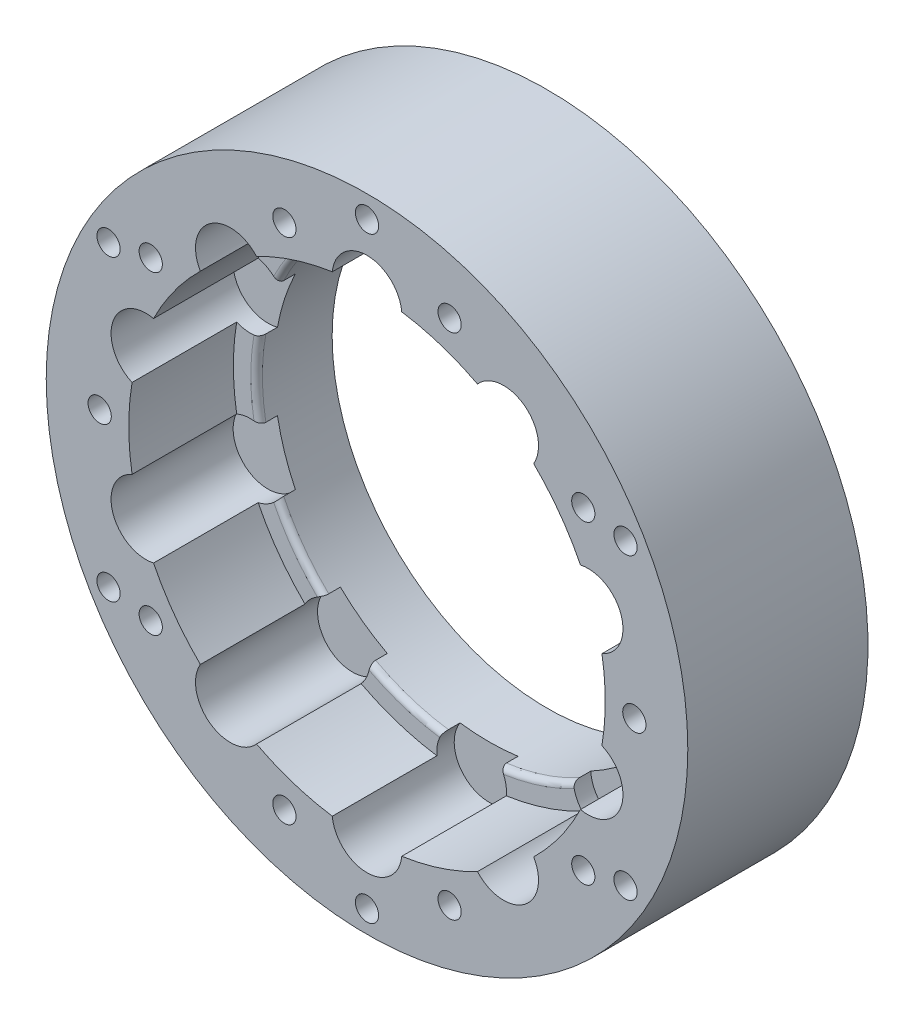
SolidWorks part; units mm, degrees
ref_plane "前视基准面" through (0, 0, 0) normal (0, 0, 1) x (1, 0, 0)
ref_plane "上视基准面" through (0, 0, 0) normal (0, 1, 0) x (1, 0, 0)
ref_plane "右视基准面" through (0, 0, 0) normal (1, 0, 0) x (0, 0, -1)
sketch "草图1" plane through (0, 0, 0) normal (0, 0, 1) x (1, 0, 0)
  circle A0 centre (0, 0) radius 27.6
  circle A1 centre (0, 0) radius 20 construction
  arc A2 (2.9916, 19.775) -> (-2.9916, 19.775) centre (0, 20) ccw
  arc A3 (-2.9916, 19.775) -> (-9.2032, 17.7567) centre (0, 0) ccw
  arc A4 (14.0437, 14.2399) -> (9.2032, 17.7567) centre (11.7557, 16.1803) ccw
  arc A5 (19.7316, 3.2657) -> (17.8827, 8.9559) centre (19.0211, 6.1803) ccw
  arc A6 (17.8827, -8.9559) -> (19.7316, -3.2657) centre (19.0211, -6.1803) ccw
  arc A7 (9.2032, -17.7567) -> (14.0437, -14.2399) centre (11.7557, -16.1803) ccw
  arc A8 (-2.9916, -19.775) -> (2.9916, -19.775) centre (0, -20) ccw
  arc A9 (-14.0437, -14.2399) -> (-9.2032, -17.7567) centre (-11.7557, -16.1803) ccw
  arc A10 (-19.7316, -3.2657) -> (-17.8827, -8.9559) centre (-19.0211, -6.1803) ccw
  arc A11 (-17.8827, 8.9559) -> (-19.7316, 3.2657) centre (-19.0211, 6.1803) ccw
  arc A12 (-9.2032, 17.7567) -> (-14.0437, 14.2399) centre (-11.7557, 16.1803) ccw
  arc A13 (-14.0437, 14.2399) -> (-17.8827, 8.9559) centre (0, 0) ccw
  arc A14 (-19.7316, 3.2657) -> (-19.7316, -3.2657) centre (0, 0) ccw
  arc A15 (-17.8827, -8.9559) -> (-14.0437, -14.2399) centre (0, 0) ccw
  arc A16 (-9.2032, -17.7567) -> (-2.9916, -19.775) centre (0, 0) ccw
  arc A17 (2.9916, -19.775) -> (9.2032, -17.7567) centre (0, 0) ccw
  arc A18 (14.0437, -14.2399) -> (17.8827, -8.9559) centre (0, 0) ccw
  arc A19 (19.7316, -3.2657) -> (19.7316, 3.2657) centre (0, 0) ccw
  arc A20 (17.8827, 8.9559) -> (14.0437, 14.2399) centre (0, 0) ccw
  arc A21 (9.2032, 17.7567) -> (2.9916, 19.775) centre (0, 0) ccw
  point P36 (0, 0)
  dimension "D1" = 55.2
  dimension "D2" = 40
  dimension "D3" = 6
  dimension "D4" = 10
extrude "凸台-拉伸1" add sketch "草图1" along normal blind 9
sketch "草图2" plane through (0, 0, 0) normal (0, 0, -1) x (-1, 0, 0)
  circle A0 centre (0, 0) radius 27.6
extrude "凸台-拉伸2" add sketch "草图2" along normal blind 3.5
sketch "草图3" plane through (0, 0, 0) normal (0, 0, 1) x (1, 0, 0)
  circle A0 centre (0, 20) radius 3
  circle A1 centre (11.7557, 16.1803) radius 3
  circle A2 centre (19.0211, 6.1803) radius 3
  circle A3 centre (19.0211, -6.1803) radius 3
  circle A4 centre (11.7557, -16.1803) radius 3
  circle A5 centre (0, -20) radius 3
  circle A6 centre (-11.7557, -16.1803) radius 3
  circle A7 centre (-19.0211, -6.1803) radius 3
  circle A8 centre (-19.0211, 6.1803) radius 3
  circle A9 centre (-11.7557, 16.1803) radius 3
  point P23 (0, 0)
  dimension "D1" = 10
extrude "切除-拉伸1" cut sketch "草图3" against normal blind 1.5
sketch "草图4" plane through (0, 0, 9) normal (0, 0, 1) x (1, 0, 0)
  line L0 (0, 0) -> (6.1803, 19.0211) construction
  line L1 (6.1803, 19.0211) -> (7.9356, 24.4231) construction
  arc A0 (9.2032, 17.7567) -> (2.9916, 19.775) centre (0, 0) ccw construction
  circle A1 centre (7.9356, 24.4231) radius 1
  circle A2 centre (20.7756, 15.0943) radius 1
  circle A3 centre (25.68, 0) radius 1
  circle A4 centre (20.7756, -15.0943) radius 1
  circle A5 centre (7.9356, -24.4231) radius 1
  circle A6 centre (-7.9356, -24.4231) radius 1
  circle A7 centre (-20.7756, -15.0943) radius 1
  circle A8 centre (-25.68, 0) radius 1
  circle A9 centre (-20.7756, 15.0943) radius 1
  circle A10 centre (-7.9356, 24.4231) radius 1
  point P28 (0, 0)
  dimension "D2" = 2
  dimension "D1" = 5.68
  dimension "D3" = 10
extrude "切除-拉伸2" cut sketch "草图4" against normal through all both and the other way through all
sketch "草图7" plane through (0, 0, -1.5) normal (0, 0, 1) x (1, 0, 0)
  circle A0 centre (0, 0) radius 18.5
  dimension "D1" = 37
extrude "切除-拉伸4" cut sketch "草图7" against normal blind 12.5
sketch "草图9" plane through (0, 0, -1.5) normal (0, 0, -1) x (-1, 0, 0)
  circle A0 centre (0, 0) radius 18.5
extrude "切除-拉伸6" cut sketch "草图9" against normal through all
sketch "草图10" plane through (0, 0, -3.5) normal (0, 0, -1) x (-1, 0, 0)
  circle A0 centre (-7.9356, 24.4231) radius 1
  circle A1 centre (7.9356, 24.4231) radius 1
  circle A2 centre (20.7756, 15.0943) radius 1
  circle A3 centre (25.68, 0) radius 1
  circle A4 centre (20.7756, -15.0943) radius 1
  circle A5 centre (7.9356, -24.4231) radius 1
  circle A6 centre (-7.9356, -24.4231) radius 1
  circle A7 centre (-20.7756, -15.0943) radius 1
  circle A8 centre (-25.68, 0) radius 1
  circle A9 centre (-20.7756, 15.0943) radius 1
  circle A10 centre (0, 0) radius 18.5
  circle A11 centre (0, 0) radius 27.6
  point P23 (0, 0)
  dimension "D1" = 10
extrude "凸台-拉伸4" add sketch "草图10" along normal blind 2
sketch "草图11" plane through (0, 0, -5.5) normal (0, 0, -1) x (-1, 0, 0)
  circle A1 centre (-7.9356, 24.4231) radius 1
  circle A2 centre (7.9356, 24.4231) radius 1
  circle A3 centre (20.7756, 15.0943) radius 1
  circle A4 centre (25.68, 0) radius 1
  circle A5 centre (20.7756, -15.0943) radius 1
  circle A6 centre (7.9356, -24.4231) radius 1
  circle A7 centre (-7.9356, -24.4231) radius 1
  circle A8 centre (-20.7756, -15.0943) radius 1
  circle A9 centre (-25.68, 0) radius 1
  circle A10 centre (-20.7756, 15.0943) radius 1
  point P24 (0, 0)
  dimension "D1" = 10
extrude "凸台-拉伸5" add sketch "草图11" against normal up to surface (14.5 mm away) up to face at (-6.9356, 24.4231, 9)
sketch "草图12" plane through (0, 0, -5.5) normal (0, 0, -1) x (-1, 0, 0)
  circle A0 centre (0, 0) radius 18.5
  circle A1 centre (0, 0) radius 27.6
extrude "凸台-拉伸6" add sketch "草图12" along normal blind 1
sketch "草图13" plane through (0, 0, 9) normal (0, 0, 1) x (1, 0, 0)
  line L0 (0, 0) -> (0, 25.68) construction
  circle A0 centre (0, 25.68) radius 1
  circle A1 centre (22.2395, 12.84) radius 1
  circle A2 centre (22.2395, -12.84) radius 1
  circle A3 centre (0, -25.68) radius 1
  circle A4 centre (-22.2395, -12.84) radius 1
  circle A5 centre (-22.2395, 12.84) radius 1
  point P16 (0, 0)
  dimension "D2" = 2
  dimension "D1" = 25.68
  dimension "D3" = 6
extrude "切除-拉伸8" cut sketch "草图13" against normal through all both and the other way through all
sketch "草图14" plane through (0, 0, 9) normal (0, 0, 1) x (1, 0, 0)
  line L0 (0, 20) -> (11.7557, 16.1803) construction
  line L1 (0, 0) -> (7.1074, 21.8743) construction
  circle A0 centre (7.1074, 21.8743) radius 1
  circle A1 centre (23, 0) radius 1
  circle A2 centre (7.1074, -21.8743) radius 1
  circle A3 centre (-18.6074, -13.5191) radius 1
  circle A4 centre (-18.6074, 13.5191) radius 1
  point P18 (0, 0)
  dimension "D2" = 2
  dimension "D1" = 23
  dimension "D3" = 5
extrude "切除-拉伸9" cut sketch "草图14" against normal blind 6
fillet "圆角1" radius 0.5 10 edges at (14.9668, 10.874, 0) (18.5, 0, 0) (14.9668, -10.874, 0) (5.7168, -17.5945, 0) (-5.7168, -17.5945, 0) (-14.9668, -10.874, 0) (-18.5, 0, 0) (-14.9668, 10.874, 0) (-5.7168, 17.5945, 0) (5.7168, 17.5945, 0)
sketch "草图15" plane through (0, 0, 9) normal (0, 0, 1) x (1, 0, 0)
  line L0 (-11.7557, 16.1803) -> (0, 20) construction
  line L1 (0, 0) -> (-7.1074, 21.8743) construction
  circle A0 centre (-7.1074, 21.8743) radius 1
  circle A1 centre (18.6074, 13.5191) radius 1
  circle A2 centre (18.6074, -13.5191) radius 1
  circle A3 centre (-7.1074, -21.8743) radius 1
  circle A4 centre (-23, 0) radius 1
  point P18 (0, 0)
  dimension "D2" = 2
  dimension "D1" = 23
  dimension "D3" = 5
extrude "切除-拉伸10" cut sketch "草图15" against normal through all both and the other way through all
sketch "草图16" plane through (0, 0, -6.5) normal (0, 0, -1) x (-1, 0, 0)
  line L0 (5.1137, 22.9173) -> (7.0138, 24.1224)
  line L1 (7.0138, 24.1224) -> (9.0075, 23.0794)
  line L2 (9.0075, 23.0794) -> (9.101, 20.8313)
  line L3 (9.101, 20.8313) -> (7.1074, 19.6243)
  line L4 (7.1074, 19.6243) -> (5.2073, 20.6692)
  line L5 (5.2073, 20.6692) -> (5.1137, 22.9173)
  line L6 (21.2668, 1.4347) -> (23.3759, 2.2184)
  line L7 (23.3759, 2.2184) -> (25.1091, 0.7837)
  line L8 (25.1091, 0.7837) -> (24.7332, -1.4347)
  line L9 (24.7332, -1.4347) -> (22.6241, -2.2184)
  line L10 (22.6241, -2.2184) -> (20.8601, -0.6953)
  line L11 (20.8601, -0.6953) -> (21.2668, 1.4347)
  line L12 (7.9363, -19.7825) -> (9.3333, -21.5463)
  line L13 (9.3333, -21.5463) -> (8.5045, -23.638)
  line L14 (8.5045, -23.638) -> (6.2785, -23.9661)
  line L15 (6.2785, -23.9661) -> (4.8814, -22.2023)
  line L16 (4.8814, -22.2023) -> (5.7849, -20.054)
  line L17 (5.7849, -20.054) -> (7.9363, -19.7825)
  line L18 (-16.3619, -13.661) -> (-17.6075, -15.5347)
  line L19 (-17.6075, -15.5347) -> (-19.8531, -15.3928)
  line L20 (-19.8531, -15.3928) -> (-20.8529, -13.3771)
  line L21 (-20.8529, -13.3771) -> (-19.6072, -11.5034)
  line L22 (-19.6072, -11.5034) -> (-17.2849, -11.6988)
  line L23 (-17.2849, -11.6988) -> (-16.3619, -13.661)
  line L24 (-18.0485, 11.3396) -> (-20.2154, 11.9453)
  line L25 (-20.2154, 11.9453) -> (-20.7743, 14.1248)
  line L26 (-20.7743, 14.1248) -> (-19.1663, 15.6985)
  line L27 (-19.1663, 15.6985) -> (-16.9994, 15.0928)
  line L28 (-16.9994, 15.0928) -> (-16.4675, 12.8238)
  line L29 (-16.4675, 12.8238) -> (-18.0485, 11.3396)
  circle A0 centre (7.1074, 21.8743) radius 2.25 construction
  point P3 (5.1137, 22.9173)
  point P6 (7.0138, 24.1224)
  point P7 (9.0075, 23.0794)
  point P8 (9.101, 20.8313)
  point P9 (7.201, 19.6262)
  point P10 (5.2073, 20.6692)
  point P11 (7.1074, 21.8743)
  point P42 (0, 0)
  dimension "D1" = 4.5
  dimension "D2" = 6
  dimension "D3" = 5
extrude "切除-拉伸11" cut sketch "草图16" against normal blind 2.5
sketch "草图17" plane through (0, 0, 9) normal (0, 0, 1) x (1, 0, 0)
  circle A0 centre (0, 0) radius 20.5
extrude "切除-拉伸12" cut sketch "草图17" against normal up to surface (9 mm away) up to face at (-5.9847, 18.4189, 0)
